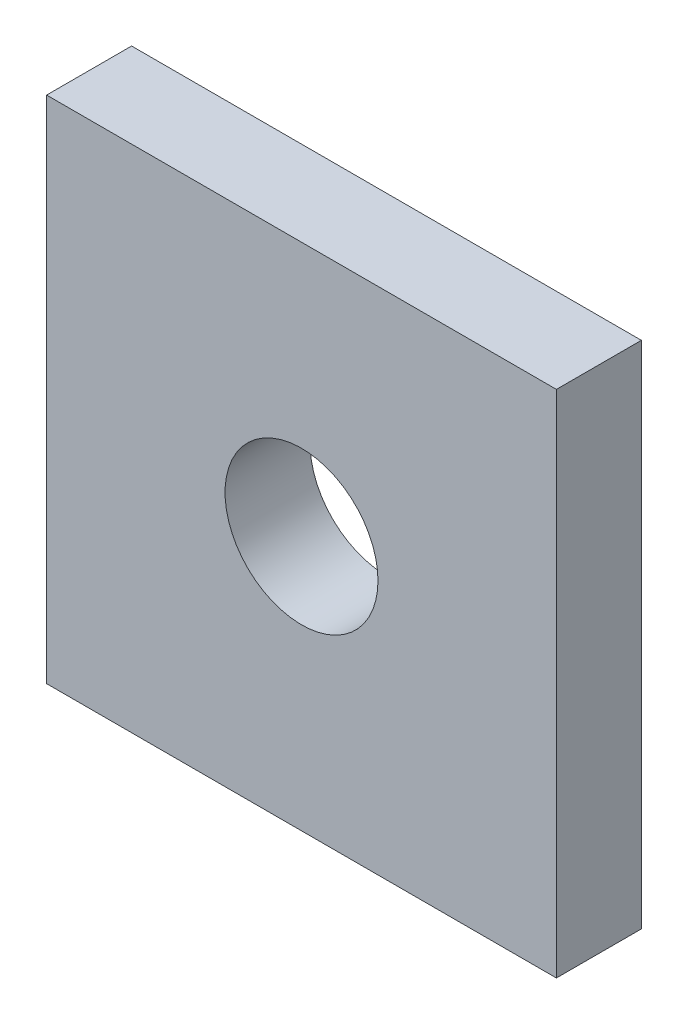
SolidWorks part; units mm, degrees
ref_plane "前视基准面" through (0, 0, 0) normal (0, 0, 1) x (1, 0, 0)
ref_plane "上视基准面" through (0, 0, 0) normal (0, 1, 0) x (1, 0, 0)
ref_plane "右视基准面" through (0, 0, 0) normal (1, 0, 0) x (0, 0, -1)
sketch "草图1" plane through (0, 0, 0) normal (0, 0, 1) x (1, 0, 0)
  line L1 (-15, 15) -> (15, 15)
  line L2 (-15, 15) -> (-15, -15)
  line L3 (-15, -15) -> (15, -15)
  line L4 (15, 15) -> (15, -15)
  line L5 (-15, 15) -> (15, -15) construction
  line L6 (-15, -15) -> (15, 15) construction
  circle A0 centre (0, 0) radius 4.5
  point P0 (0, 0)
  dimension "D3" = 9
  dimension "D1" = 30
  dimension "D2" = 30
extrude "凸台-拉伸1" add sketch "草图1" along normal blind 5
